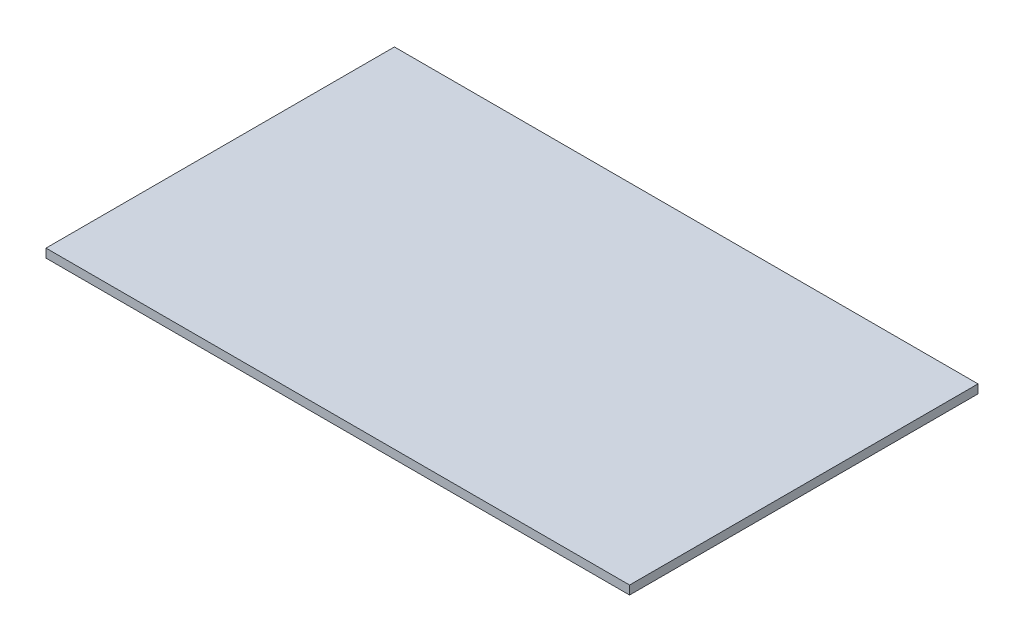
SolidWorks part; units mm, degrees
ref_plane "Front Plane" through (0, 0, 0) normal (0, 0, 1) x (1, 0, 0)
ref_plane "Top Plane" through (0, 0, 0) normal (0, 1, 0) x (1, 0, 0)
ref_plane "Right Plane" through (0, 0, 0) normal (1, 0, 0) x (0, 0, -1)
sketch "Sketch1" plane through (0, 0, 0) normal (0, 1, 0) x (1, 0, 0)
  line L1 (0, 0) -> (670, 0)
  line L2 (0, 0) -> (0, 400)
  line L3 (0, 400) -> (670, 400)
  line L4 (670, 0) -> (670, 400)
  dimension "D1" = 400
  dimension "D2" = 670
extrude "Extrude1" add sketch "Sketch1" along normal blind 10
